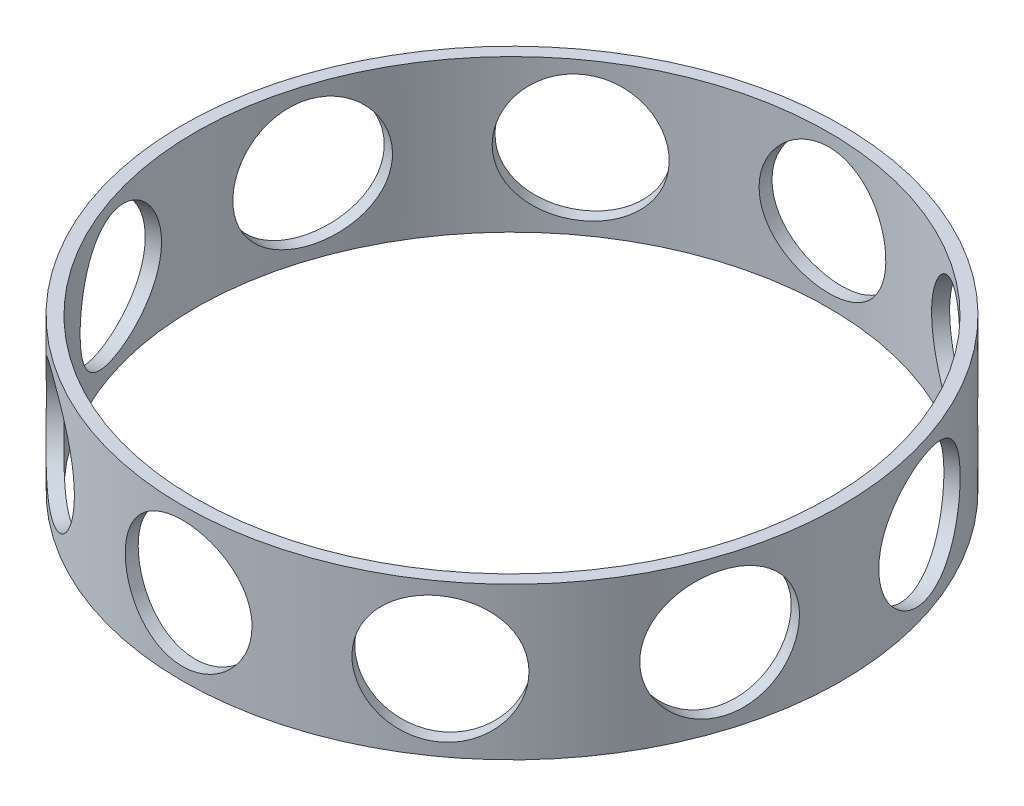
SolidWorks part; units mm, degrees
ref_plane "Front Plane" through (0, 0, 0) normal (0, 0, 1) x (1, 0, 0)
ref_plane "Top Plane" through (0, 0, 0) normal (0, 1, 0) x (1, 0, 0)
ref_plane "Right Plane" through (0, 0, 0) normal (1, 0, 0) x (0, 0, -1)
sketch "Sketch1" plane through (0, 0, 0) normal (0, 1, 0) x (1, 0, 0)
  circle A1 centre (0, 0) radius 12.5
  circle A2 centre (0, 0) radius 13
  dimension "D1" = 26
  dimension "D2" = 25
extrude "Boss-Extrude2" add sketch "Sketch1" along normal blind 6 contours A1 | A2
sketch "Sketch5" plane through (0, 0, 0) normal (0, 0, 1) x (1, 0, 0)
  line L0 (12.5, 6) -> (-12.5, 6) construction
  circle A0 centre (0, 3) radius 2.5
  dimension "D1" = 5
  dimension "D2" = 3
extrude "Cut-Extrude1" cut sketch "Sketch5" against normal through all both and the other way through all
pattern_circular "CirPattern1" count 5 over 360 about axis through (0, 6, 0) along (0, -1, 0) of "Cut-Extrude1"
